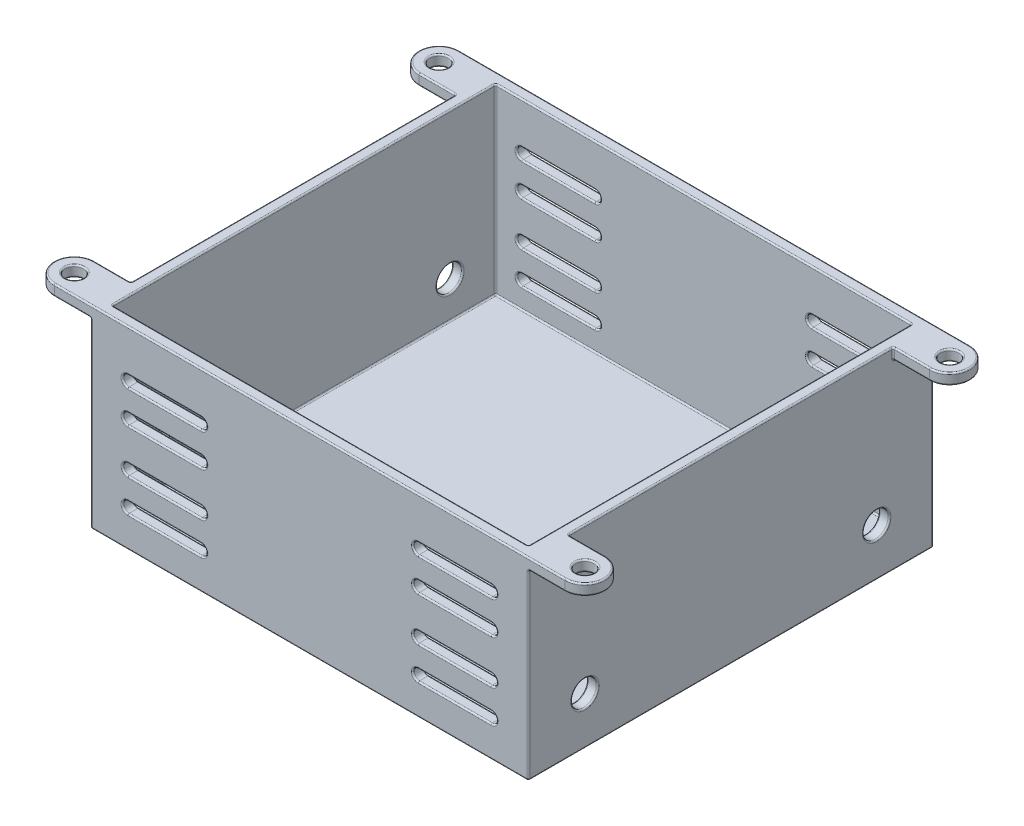
SolidWorks part; units mm, degrees
ref_plane "Front Plane" through (0, 0, 0) normal (0, 0, 1) x (1, 0, 0)
ref_plane "Top Plane" through (0, 0, 0) normal (0, 1, 0) x (1, 0, 0)
ref_plane "Right Plane" through (0, 0, 0) normal (1, 0, 0) x (0, 0, -1)
sketch "Sketch1" plane through (0, 0, 0) normal (0, 1, 0) x (1, 0, 0)
  line L0 (-35, 27.75) -> (35, 27.75) construction
  line L1 (-35, 25) -> (35, 25) construction
  line L2 (-35, 25) -> (-35, -25) construction
  line L3 (-35, -25) -> (35, -25) construction
  line L4 (35, 25) -> (35, -25) construction
  line L5 (-35, 25) -> (35, -25) construction
  line L6 (-35, -25) -> (35, 25) construction
  line L7 (-30, 27.75) -> (-30, -27.75)
  line L8 (35, -27.75) -> (-35, -27.75) construction
  line L9 (-30, -27.75) -> (30, -27.75)
  line L10 (30, -27.75) -> (30, 27.75)
  line L11 (30, 27.75) -> (-30, 27.75)
  line L12 (-35, 22.25) -> (-30, 22.25)
  line L13 (35, 22.25) -> (30, 22.25)
  line L14 (-35, -22.25) -> (-30, -22.25)
  line L15 (35, -22.25) -> (30, -22.25)
  circle A0 centre (-35, 25) radius 1.25
  circle A1 centre (35, 25) radius 1.25
  circle A2 centre (35, -25) radius 1.25
  circle A3 centre (-35, -25) radius 1.25
  circle A4 centre (-35, 25) radius 2.75
  circle A5 centre (35, 25) radius 2.75
  circle A6 centre (35, -25) radius 2.75
  circle A7 centre (-35, -25) radius 2.75
  point P0 (0, 0)
  point P28 (0, 27.75)
  dimension "D3" = 2.5
  dimension "D1" = 70
  dimension "D2" = 50
  dimension "D5" = 60
  dimension "D4" = 1.5
sketch "Sketch9" plane through (0, 0, 0) normal (0, 1, 0) x (1, 0, 0)
  line L0 (-30, -27.75) -> (30, -27.75) construction
  line L1 (30, -27.75) -> (30, 27.75) construction
  line L2 (30, 27.75) -> (-30, 27.75) construction
  line L3 (-30, 27.75) -> (-30, -27.75) construction
  line L4 (-30, -27.75) -> (30, -27.75)
  line L5 (30, -27.75) -> (30, 27.75)
  line L6 (30, 27.75) -> (-30, 27.75)
  line L7 (-30, 27.75) -> (-30, -27.75)
  line L8 (28.5, 26.25) -> (-28.5, 26.25)
  line L9 (-28.5, 26.25) -> (-28.5, -26.25)
  line L10 (-28.5, -26.25) -> (28.5, -26.25)
  line L11 (28.5, -26.25) -> (28.5, 26.25)
  dimension "D1" = 1.5
extrude "Boss-Extrude6" add sketch "Sketch9" against normal blind 25
sketch "Sketch10" plane through (0, -25, 0) normal (0, -1, 0) x (1, 0, 0)
  line L4 (-30, 27.75) -> (-30, -27.75)
  line L5 (-30, -27.75) -> (30, -27.75)
  line L6 (30, -27.75) -> (30, 27.75)
  line L7 (30, 27.75) -> (-30, 27.75)
  line L8 (-30, 27.75) -> (-30, -27.75)
  line L9 (-30, -27.75) -> (30, -27.75)
  line L10 (30, -27.75) -> (30, 27.75)
  line L11 (30, 27.75) -> (-30, 27.75)
  dimension "D1" = 0
extrude "Boss-Extrude7" add sketch "Sketch10" along normal blind 1.5
sketch "Sketch11" plane through (0, 0, 0) normal (0, 1, 0) x (1, 0, 0)
  line L0 (-35, -22.25) -> (-30, -22.25) construction
  line L1 (35, 22.25) -> (30, 22.25) construction
  line L2 (-35, 22.25) -> (-30, 22.25) construction
  line L3 (35, -22.25) -> (30, -22.25) construction
  line L4 (35, -27.75) -> (-35, -27.75) construction
  line L5 (-35, 27.75) -> (35, 27.75) construction
  line L6 (35, -27.75) -> (30, -27.75)
  line L7 (-35, 27.75) -> (-30, 27.75)
  line L8 (-35, -22.25) -> (-30, -22.25)
  line L9 (35, -22.25) -> (30, -22.25)
  line L10 (35, 22.25) -> (30, 22.25)
  line L11 (-35, 22.25) -> (-30, 22.25)
  line L12 (30, -27.75) -> (30, 27.75) construction
  line L13 (-30, 27.75) -> (-30, -27.75) construction
  line L14 (30, -27.75) -> (30, -22.25)
  line L15 (-30, 27.75) -> (-30, 22.25)
  line L16 (30, 22.25) -> (30, 27.75)
  line L17 (-30, -22.25) -> (-30, -27.75)
  line L18 (30, 27.75) -> (35, 27.75)
  line L19 (-30, -27.75) -> (-35, -27.75)
  circle A0 centre (35, 25) radius 1.25 construction
  circle A1 centre (35, 25) radius 2.75 construction
  circle A2 centre (-35, 25) radius 2.75 construction
  circle A3 centre (-35, 25) radius 1.25 construction
  circle A4 centre (-35, -25) radius 2.75 construction
  circle A5 centre (-35, -25) radius 1.25 construction
  circle A6 centre (35, -25) radius 2.75 construction
  circle A7 centre (35, -25) radius 1.25 construction
  circle A8 centre (-35, -25) radius 1.25
  arc A9 (-35, -22.25) -> (-35, -27.75) centre (-35, -25) ccw
  circle A10 centre (35, -25) radius 1.25
  arc A11 (35, -27.75) -> (35, -22.25) centre (35, -25) ccw
  circle A12 centre (35, 25) radius 1.25
  arc A13 (35, 22.25) -> (35, 27.75) centre (35, 25) ccw
  circle A14 centre (-35, 25) radius 1.25
  arc A15 (-35, 27.75) -> (-35, 22.25) centre (-35, 25) ccw
extrude "Boss-Extrude8" add sketch "Sketch11" against normal blind 1.5
sketch "Sketch12" plane through (0, 0, 0) normal (0, 0, 1) x (1, 0, 0)
  line L0 (-30, -14) -> (30, -14) construction
  line L1 (-30, -26.5) -> (-30, -1.5) construction
  line L2 (30, -26.5) -> (30, -1.5) construction
  line L3 (-24.8963, -6.5) -> (-14.8963, -6.5) construction
  line L4 (-24.8963, -5.75) -> (-14.8963, -5.75)
  line L5 (-24.8963, -7.25) -> (-14.8963, -7.25)
  line L6 (-24.8963, -11) -> (-14.8963, -11) construction
  line L7 (-24.8963, -10.25) -> (-14.8963, -10.25)
  line L8 (-24.8963, -11.75) -> (-14.8963, -11.75)
  line L9 (0, -14) -> (0, -23.1353) construction
  line L10 (-24.8963, -17) -> (-14.8963, -17) construction
  line L11 (-24.8963, -17.75) -> (-14.8963, -17.75)
  line L12 (-24.8963, -16.25) -> (-14.8963, -16.25)
  line L13 (-24.8963, -21.5) -> (-14.8963, -21.5) construction
  line L14 (-24.8963, -22.25) -> (-14.8963, -22.25)
  line L15 (-24.8963, -20.75) -> (-14.8963, -20.75)
  line L16 (24.8963, -21.5) -> (14.8963, -21.5) construction
  line L17 (24.8963, -22.25) -> (14.8963, -22.25)
  line L18 (24.8963, -20.75) -> (14.8963, -20.75)
  line L19 (24.8963, -17) -> (14.8963, -17) construction
  line L20 (24.8963, -17.75) -> (14.8963, -17.75)
  line L21 (24.8963, -16.25) -> (14.8963, -16.25)
  line L22 (24.8963, -11) -> (14.8963, -11) construction
  line L23 (24.8963, -10.25) -> (14.8963, -10.25)
  line L24 (24.8963, -11.75) -> (14.8963, -11.75)
  line L25 (24.8963, -6.5) -> (14.8963, -6.5) construction
  line L26 (24.8963, -5.75) -> (14.8963, -5.75)
  line L27 (24.8963, -7.25) -> (14.8963, -7.25)
  arc A0 (-24.8963, -5.75) -> (-24.8963, -7.25) centre (-24.8963, -6.5) ccw
  arc A1 (-14.8963, -7.25) -> (-14.8963, -5.75) centre (-14.8963, -6.5) ccw
  arc A2 (-24.8963, -10.25) -> (-24.8963, -11.75) centre (-24.8963, -11) ccw
  arc A3 (-14.8963, -11.75) -> (-14.8963, -10.25) centre (-14.8963, -11) ccw
  arc A4 (-24.8963, -17.75) -> (-24.8963, -16.25) centre (-24.8963, -17) cw
  arc A5 (-14.8963, -16.25) -> (-14.8963, -17.75) centre (-14.8963, -17) cw
  arc A6 (-24.8963, -22.25) -> (-24.8963, -20.75) centre (-24.8963, -21.5) cw
  arc A7 (-14.8963, -20.75) -> (-14.8963, -22.25) centre (-14.8963, -21.5) cw
  arc A8 (24.8963, -22.25) -> (24.8963, -20.75) centre (24.8963, -21.5) ccw
  arc A9 (14.8963, -20.75) -> (14.8963, -22.25) centre (14.8963, -21.5) ccw
  arc A10 (24.8963, -17.75) -> (24.8963, -16.25) centre (24.8963, -17) ccw
  arc A11 (14.8963, -16.25) -> (14.8963, -17.75) centre (14.8963, -17) ccw
  arc A12 (24.8963, -10.25) -> (24.8963, -11.75) centre (24.8963, -11) cw
  arc A13 (14.8963, -11.75) -> (14.8963, -10.25) centre (14.8963, -11) cw
  arc A14 (24.8963, -5.75) -> (24.8963, -7.25) centre (24.8963, -6.5) cw
  arc A15 (14.8963, -7.25) -> (14.8963, -5.75) centre (14.8963, -6.5) cw
  point P8 (-19.8963, -6.5)
  point P16 (-19.8963, -11)
  point P25 (-19.8963, -17)
  point P32 (-19.8963, -21.5)
  point P39 (19.8963, -21.5)
  point P46 (19.8963, -17)
  point P53 (19.8963, -11)
  point P60 (19.8963, -6.5)
  dimension "D1" = 10
  dimension "D2" = 1.5
  dimension "D3" = 19.8963
  dimension "D4" = 7.5
  dimension "D5" = 4.5
extrude "Cut-Extrude1" cut sketch "Sketch12" against normal up to surface and the other way up to surface up to face at (0, -7.375, -27.75) other way up to face at (0, -7.375, 27.75)
sketch "Sketch13" plane through (0, 0, 0) normal (1, 0, 0) x (0, 0, -1)
  line L0 (0, 0) -> (0, -20) construction
  line L1 (0, -20) -> (-20, -20) construction
  circle A0 centre (-20, -20) radius 1.75
  circle A1 centre (20, -20) radius 1.75
  dimension "D1" = 3.5
  dimension "D2" = 20
  dimension "D3" = 20
extrude "Cut-Extrude2" cut sketch "Sketch13" along normal up to surface and the other way up to surface up to face at (30, -7.375, 0) other way up to face at (-30, -7.375, 0)
fillet "Fillet1" radius 0.2 196 edges at (30, -20, -21.75) (-30, -20, -18.25) (-30, -20, 21.75) (30, -20, 18.25) (-28.5, -20, -18.25) (28.5, -20, -21.75) (-28.5, -20, 21.75) (28.5, -20, 18.25) (25.6463, -6.5, -27.75) (19.8963, -7.25, -27.75) (14.1463, -6.5, -27.75) (19.8963, -5.75, -27.75) (14.1463, -6.5, 27.75) (19.8963, -5.75, 27.75) (25.6463, -6.5, 27.75) (19.8963, -7.25, 27.75) (25.6463, -11, -27.75) (19.8963, -11.75, -27.75) (14.1463, -11, -27.75) (19.8963, -10.25, -27.75) (14.1463, -11, 27.75) (19.8963, -10.25, 27.75) (25.6463, -11, 27.75) (19.8963, -11.75, 27.75) (25.6463, -17, -27.75) (19.8963, -17.75, -27.75) (14.1463, -17, -27.75) (19.8963, -16.25, -27.75) (14.1463, -17, 27.75) (19.8963, -16.25, 27.75) (25.6463, -17, 27.75) (19.8963, -17.75, 27.75) (25.6463, -21.5, -27.75) (19.8963, -22.25, -27.75) (14.1463, -21.5, -27.75) (19.8963, -20.75, -27.75) (14.1463, -21.5, 27.75) (19.8963, -20.75, 27.75) (25.6463, -21.5, 27.75) (19.8963, -22.25, 27.75) (-25.6463, -21.5, -27.75) (-19.8963, -20.75, -27.75) (-14.1463, -21.5, -27.75) (-19.8963, -22.25, -27.75) (-14.1463, -21.5, 27.75) (-19.8963, -22.25, 27.75) (-25.6463, -21.5, 27.75) (-19.8963, -20.75, 27.75) (-25.6463, -17, -27.75) (-19.8963, -16.25, -27.75) (-14.1463, -17, -27.75) (-19.8963, -17.75, -27.75) (-14.1463, -17, 27.75) (-19.8963, -17.75, 27.75) (-25.6463, -17, 27.75) (-19.8963, -16.25, 27.75) (-25.6463, -11, -27.75) (-19.8963, -10.25, -27.75) (-14.1463, -11, -27.75) (-19.8963, -11.75, -27.75) (-14.1463, -11, 27.75) (-19.8963, -11.75, 27.75) (-25.6463, -11, 27.75) (-19.8963, -10.25, 27.75) (-19.8963, -5.75, 27.75) (-25.6463, -6.5, 27.75) (-19.8963, -7.25, 27.75) (-14.1463, -6.5, 27.75) (-19.8963, -7.25, -27.75) (-14.1463, -6.5, -27.75) (-19.8963, -5.75, -27.75) (-25.6463, -6.5, -27.75) (-25.6463, -6.5, 26.25) (-19.8963, -5.75, 26.25) (-14.1463, -6.5, 26.25) (-19.8963, -7.25, 26.25) (25.6463, -6.5, 26.25) (19.8963, -7.25, 26.25) (14.1463, -6.5, 26.25) (19.8963, -5.75, 26.25) (25.6463, -11, 26.25) (19.8963, -11.75, 26.25) (14.1463, -11, 26.25) (19.8963, -10.25, 26.25) (25.6463, -17, 26.25) (19.8963, -17.75, 26.25) (14.1463, -17, 26.25) (19.8963, -16.25, 26.25) (25.6463, -21.5, 26.25) (19.8963, -22.25, 26.25) (14.1463, -21.5, 26.25) (19.8963, -20.75, 26.25) (-25.6463, -21.5, 26.25) (-19.8963, -20.75, 26.25) (-14.1463, -21.5, 26.25) (-19.8963, -22.25, 26.25) (-25.6463, -17, 26.25) (-19.8963, -16.25, 26.25) (-14.1463, -17, 26.25) (-19.8963, -17.75, 26.25) (-25.6463, -11, 26.25) (-19.8963, -10.25, 26.25) (-14.1463, -11, 26.25) (-19.8963, -11.75, 26.25) (-30, -0.75, -22.25) (-32.5, -1.5, -27.75) (-30, -1.5, -25) (-32.5, -1.5, -22.25) (-37.75, -1.5, -25) (-32.5, 0, -22.25) (-37.75, 0, -25) (-35, -1.5, -23.75) (-35, 0, -23.75) (30, -0.75, -22.25) (32.5, -1.5, -22.25) (30, -1.5, -25) (32.5, -1.5, -27.75) (37.75, -1.5, -25) (32.5, 0, -22.25) (37.75, 0, -25) (35, -1.5, -23.75) (35, 0, -23.75) (30, -0.75, 22.25) (32.5, -1.5, 27.75) (30, -1.5, 25) (32.5, -1.5, 22.25) (37.75, -1.5, 25) (32.5, 0, 22.25) (37.75, 0, 25) (35, -1.5, 26.25) (35, 0, 26.25) (-35, -1.5, 26.25) (-35, 0, 26.25) (-37.75, 0, 25) (-37.75, -1.5, 25) (-32.5, 0, 22.25) (-32.5, -1.5, 22.25) (-32.5, -1.5, 27.75) (-30, -1.5, 25) (-30, -0.75, 22.25) (0, -26.5, 27.75) (-30, -26.5, 0) (0, -26.5, -27.75) (30, -26.5, 0) (28.5, 0, 0) (28.5, -25, 0) (0, 0, -26.25) (0, -25, -26.25) (-28.5, 0, 0) (-28.5, -25, 0) (0, 0, 26.25) (0, -25, 26.25) (28.5, -12.5, -26.25) (-28.5, -12.5, -26.25) (-28.5, -12.5, 26.25) (28.5, -12.5, 26.25) (-30, 0, 0) (0, 0, 27.75) (30, 0, 0) (0, 0, -27.75) (-30, -14, 27.75) (30, -14, -27.75) (-30, -14, -27.75) (-25.6463, -6.5, -26.25) (-19.8963, -5.75, -26.25) (-14.1463, -6.5, -26.25) (-19.8963, -7.25, -26.25) (25.6463, -6.5, -26.25) (19.8963, -7.25, -26.25) (14.1463, -6.5, -26.25) (19.8963, -5.75, -26.25) (25.6463, -11, -26.25) (19.8963, -11.75, -26.25) (14.1463, -11, -26.25) (19.8963, -10.25, -26.25) (25.6463, -17, -26.25) (19.8963, -17.75, -26.25) (14.1463, -17, -26.25) (19.8963, -16.25, -26.25) (25.6463, -21.5, -26.25) (19.8963, -22.25, -26.25) (14.1463, -21.5, -26.25) (19.8963, -20.75, -26.25) (-25.6463, -21.5, -26.25) (-19.8963, -20.75, -26.25) (-14.1463, -21.5, -26.25) (-19.8963, -22.25, -26.25) (-25.6463, -17, -26.25) (-19.8963, -16.25, -26.25) (-14.1463, -17, -26.25) (-19.8963, -17.75, -26.25) (-25.6463, -11, -26.25) (-19.8963, -10.25, -26.25) (-14.1463, -11, -26.25) (-19.8963, -11.75, -26.25) (30, -14, 27.75)
